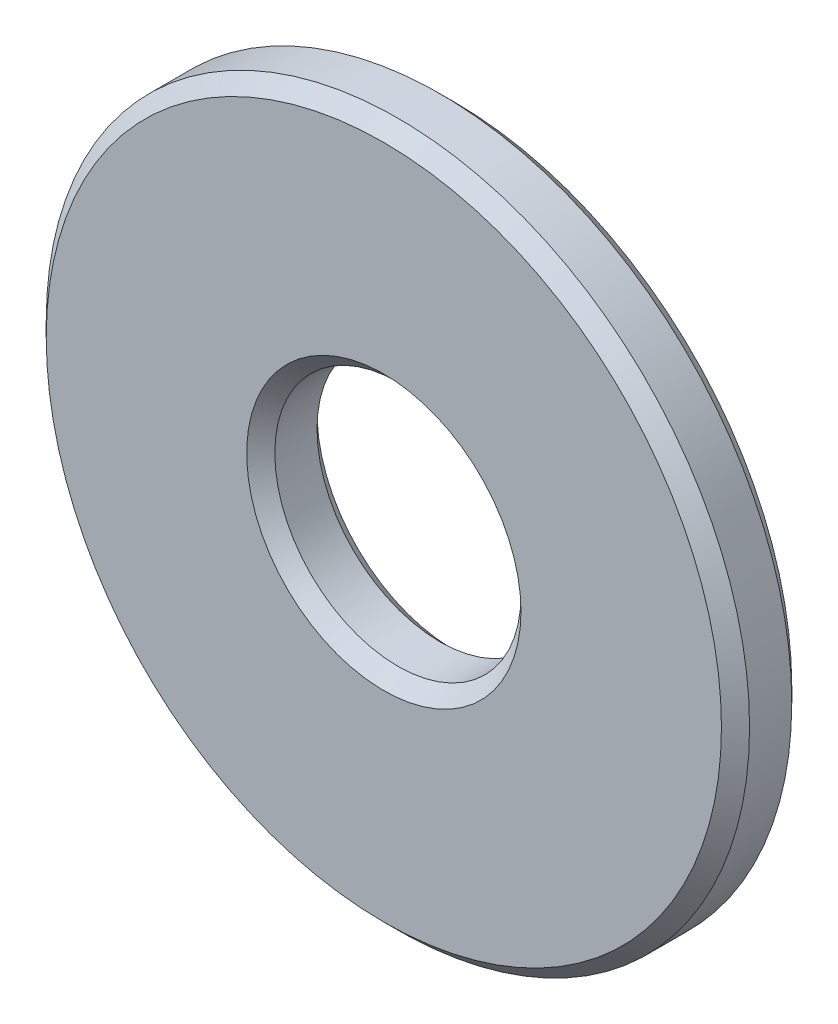
SolidWorks part; units mm, degrees
ref_plane "Front Plane" through (0, 0, 0) normal (0, 0, 1) x (1, 0, 0)
ref_plane "Top Plane" through (0, 0, 0) normal (0, 1, 0) x (1, 0, 0)
ref_plane "Right Plane" through (0, 0, 0) normal (1, 0, 0) x (0, 0, -1)
sketch "Sketch1" plane through (0, 0, 0) normal (0, 0, 1) x (1, 0, 0)
  circle A0 centre (0, 0) radius 1.75
  circle A1 centre (0, 0) radius 5
  dimension "D1" = 3.5
  dimension "D2" = 10
extrude "Boss-Extrude1" add sketch "Sketch1" along normal blind 1
chamfer "Chamfer1" distance 0.2 angle 45 4 edges at (1.75, 0, 0) (5, 0, 0) (1.75, 0, 1) (5, 0, 1)
